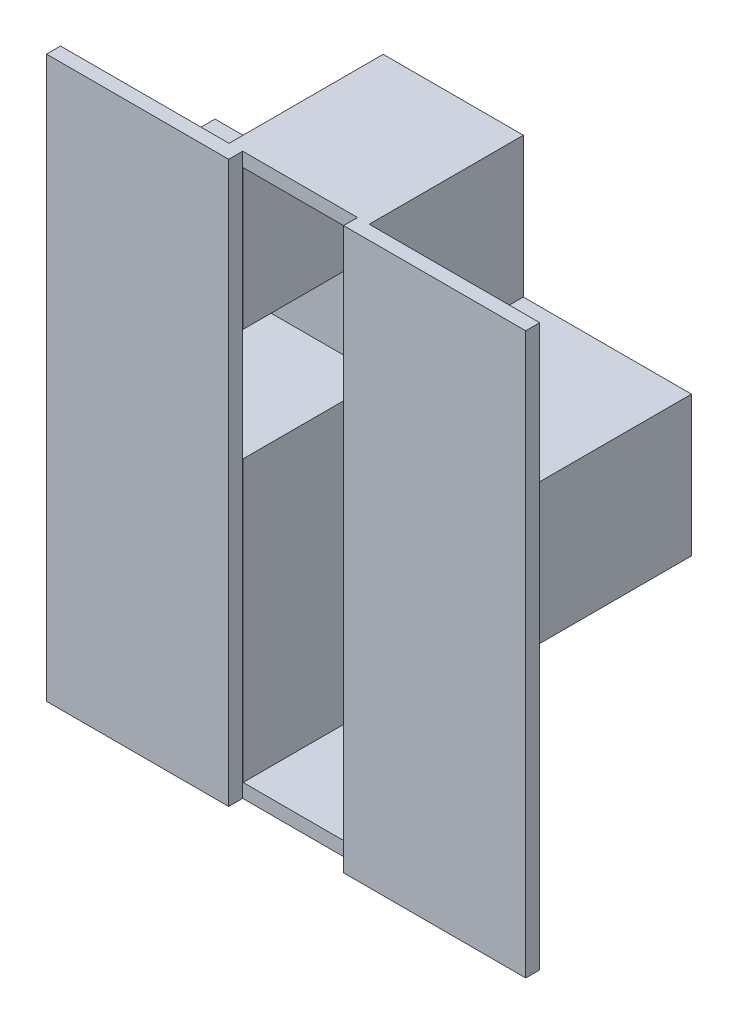
SolidWorks part; units mm, degrees
ref_plane "Plan de face" through (0, 0, 0) normal (0, 0, 1) x (1, 0, 0)
ref_plane "Plan de dessus" through (0, 0, 0) normal (0, 1, 0) x (1, 0, 0)
ref_plane "Plan de droite" through (0, 0, 0) normal (1, 0, 0) x (0, 0, -1)
sketch "Esquisse1" plane through (0, 0, 0) normal (0, 0, 1) x (1, 0, 0)
  line L0 (-50, 100) -> (-110, 100)
  line L1 (0, 0) -> (-50, 0)
  line L2 (0, 0) -> (0, 100)
  line L3 (-50, 150) -> (-110, 150)
  line L4 (-50, 0) -> (-50, 100)
  line L5 (60, 100) -> (0, 100)
  line L6 (60, 100) -> (60, 150)
  line L7 (60, 150) -> (0, 150)
  line L8 (-110, 100) -> (-110, 150)
  line L10 (-50, 150) -> (-50, 200)
  line L11 (-50, 200) -> (0, 200)
  line L12 (0, 150) -> (0, 200)
  dimension "D1" = 50
  dimension "D2" = 60
  dimension "D3" = 60
  dimension "D4" = 50
  dimension "D5" = 100
  dimension "D6" = 50
extrude "Boss.-Extru.2" add sketch "Esquisse1" along normal blind 5
sketch "Esquisse2" plane through (0, 0, 5) normal (0, 0, 1) x (1, 0, 0)
  line L20 (-110, 150) -> (-110, 100)
  line L21 (-50, 150) -> (-110, 150)
  line L22 (0, 150) -> (0, 200)
  line L23 (0, 200) -> (-50, 200)
  line L24 (-50, 200) -> (-50, 150)
  line L25 (-110, 150) -> (-110, 100)
  line L26 (-50, 150) -> (-110, 150)
  line L27 (0, 150) -> (0, 200)
  line L28 (0, 200) -> (-50, 200)
  line L29 (-50, 200) -> (-50, 150)
  line L53 (-105, 145) -> (-105, 105)
  line L54 (-105, 105) -> (-45, 105)
  line L55 (-45, 105) -> (-45, 5)
  line L56 (-45, 5) -> (-5, 5)
  line L57 (-5, 5) -> (-5, 105)
  line L58 (-5, 105) -> (55, 105)
  line L59 (55, 105) -> (55, 145)
  line L60 (60, 150) -> (0, 150)
  line L61 (60, 100) -> (60, 150)
  line L62 (0, 100) -> (60, 100)
  line L63 (0, 0) -> (0, 100)
  line L64 (-50, 0) -> (0, 0)
  line L65 (-50, 100) -> (-50, 0)
  line L66 (-110, 100) -> (-50, 100)
  line L67 (60, 150) -> (0, 150)
  line L68 (60, 100) -> (60, 150)
  line L69 (0, 100) -> (60, 100)
  line L70 (0, 0) -> (0, 100)
  line L71 (-50, 0) -> (0, 0)
  line L72 (-50, 100) -> (-50, 0)
  line L73 (-110, 100) -> (-50, 100)
  line L74 (55, 145) -> (-5, 145)
  line L75 (-5, 145) -> (-5, 195)
  line L76 (-5, 195) -> (-45, 195)
  line L77 (-45, 195) -> (-45, 145)
  line L78 (-45, 145) -> (-105, 145)
  dimension "D1" = 0
  dimension "D2" = 0
  dimension "D3" = 5
extrude "Boss.-Extru.3" add sketch "Esquisse2" along normal blind 50
sketch "Esquisse3" plane through (0, 0, 55) normal (0, 0, 1) x (1, 0, 0)
  line L0 (-50, 0) -> (0, 0) construction
  line L1 (-45.136, 0) -> (-110.136, 0)
  line L2 (-45.136, 0) -> (-45.136, 200)
  line L3 (-45.136, 200) -> (-110.136, 200)
  line L4 (-110.136, 0) -> (-110.136, 200)
  dimension "D1" = 200
  dimension "D2" = 65
extrude "Boss.-Extru.7" add sketch "Esquisse3" along normal blind 5 contours L4 L3 L2 L1
sketch "Esquisse8" plane through (0, 0, 55) normal (0, 0, 1) x (1, 0, 0)
  line L0 (0, 200) -> (-45.136, 200) construction
  line L1 (-4.1491, 200) -> (60.8509, 200)
  line L2 (-4.1491, 200) -> (-4.1491, 0)
  line L3 (-4.1491, 0) -> (60.8509, 0)
  line L4 (60.8509, 200) -> (60.8509, 0)
  dimension "D1" = 200
  dimension "D2" = 65
extrude "Boss.-Extru.8" add sketch "Esquisse8" along normal blind 5
